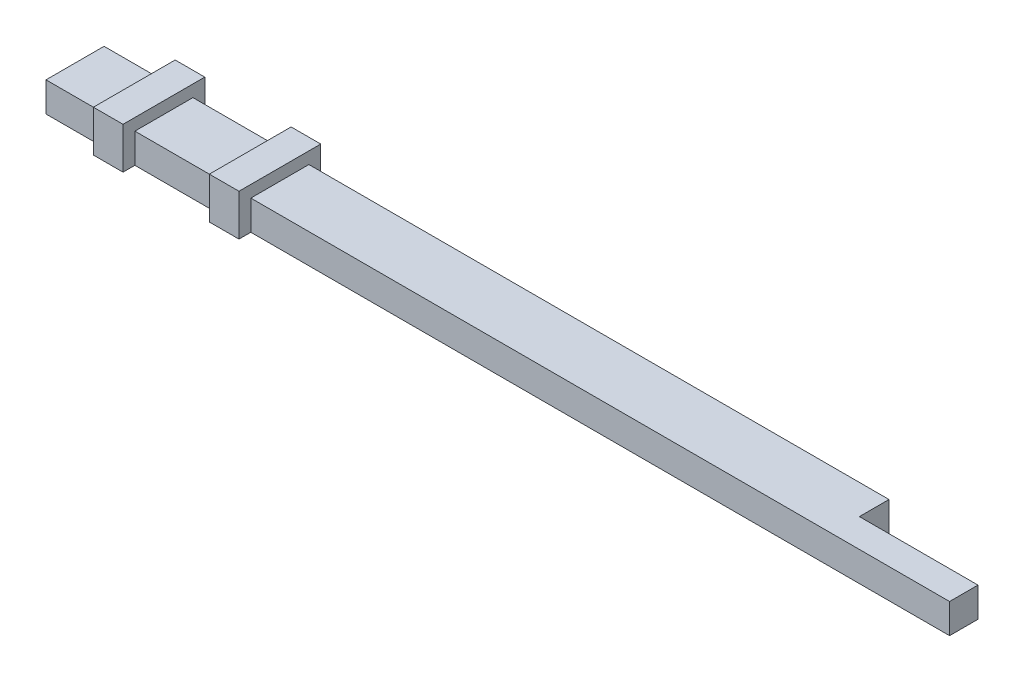
SolidWorks part; units mm, degrees
ref_plane "Front Plane" through (0, 0, 0) normal (0, 0, 1) x (1, 0, 0)
ref_plane "Top Plane" through (0, 0, 0) normal (0, 1, 0) x (1, 0, 0)
ref_plane "Right Plane" through (0, 0, 0) normal (1, 0, 0) x (0, 0, -1)
sketch "Sketch1" plane through (0, 0, 0) normal (0, 1, 0) x (1, 0, 0)
  line L0 (132.4815, 9.8) -> (132.4815, 4.8)
  line L1 (0, 0) -> (142.5, 0)
  line L2 (0, 0) -> (0, 9.8)
  line L3 (0, 9.8) -> (132.4815, 9.8)
  line L5 (142.5, 0) -> (152.5, 0)
  line L7 (142.4815, 4.8) -> (152.5, 4.8)
  line L8 (152.5, 0) -> (152.5, 4.8)
  line L9 (132.4815, 4.8) -> (142.4815, 4.8)
  dimension "D1" = 142.5
  dimension "D2" = 9.8
  dimension "D3" = 10
  dimension "D4" = 10
  dimension "D5" = 4.8
extrude "Boss-Extrude1" add sketch "Sketch1" along normal blind 5
ref_plane "Plane1" through (10, 0, 0) normal (-1, 0, 0) x (0, 0, 1)
sketch "Sketch2" plane through (10, 0, 0) normal (-1, 0, 0) x (0, 0, 1)
  line L0 (-9.8, 5) -> (0, 5) construction
  line L1 (-11.8, 7) -> (2, 7)
  line L2 (-11.8, 7) -> (-11.8, 0)
  line L3 (-11.8, 0) -> (2, 0)
  line L4 (2, 7) -> (2, 0)
  line L5 (-9.8, 0) -> (0, 0) construction
  line L6 (0, 5) -> (0, 0) construction
  line L7 (-9.8, 5) -> (-9.8, 0) construction
  dimension "D1" = 2
  dimension "D2" = 0
  dimension "D3" = 2
  dimension "D4" = 2
extrude "Boss-Extrude2" add sketch "Sketch2" against normal blind 5
ref_plane "Plane2" through (34.57, 0, 0) normal (1, 0, 0) x (0, 0, -1)
sketch "Sketch3" plane through (34.57, 0, 0) normal (1, 0, 0) x (0, 0, -1)
  line L1 (-2, 7) -> (11.8, 7)
  line L2 (-2, 7) -> (-2, 0)
  line L3 (-2, 0) -> (11.8, 0)
  line L4 (11.8, 7) -> (11.8, 0)
extrude "Boss-Extrude3" add sketch "Sketch3" against normal blind 5
